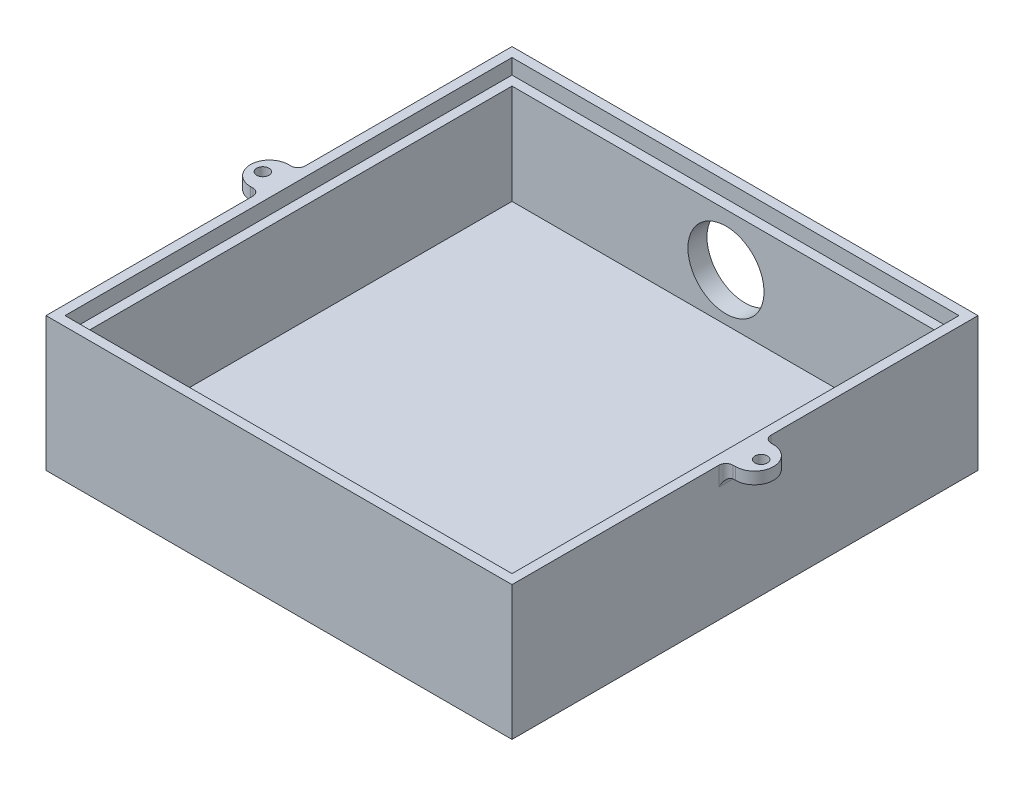
SolidWorks part; units mm, degrees
ref_plane "Front Plane" through (0, 0, 0) normal (0, 0, 1) x (1, 0, 0)
ref_plane "Top Plane" through (0, 0, 0) normal (0, 1, 0) x (1, 0, 0)
ref_plane "Right Plane" through (0, 0, 0) normal (1, 0, 0) x (0, 0, -1)
sketch "Sketch1" plane through (0, 0, 0) normal (0, 1, 0) x (1, 0, 0)
  line L1 (-49, 49) -> (49, 49)
  line L2 (-49, 49) -> (-49, -49)
  line L3 (-49, -49) -> (49, -49)
  line L4 (49, 49) -> (49, -49)
  line L5 (-49, 49) -> (49, -49) construction
  line L6 (-49, -49) -> (49, 49) construction
  point P0 (0, 0)
  dimension "D1" = 98
  dimension "D2" = 98
extrude "Boss-Extrude1" add sketch "Sketch1" along normal blind 30
sketch "Sketch2" plane through (0, 30, 0) normal (0, 1, 0) x (1, 0, 0)
  line L1 (-47, 47) -> (47, 47)
  line L2 (-47, 47) -> (-47, -47)
  line L3 (-47, -47) -> (47, -47)
  line L4 (47, 47) -> (47, -47)
  line L5 (-47, 47) -> (47, -47) construction
  line L6 (-47, -47) -> (47, 47) construction
  point P0 (0, 0)
  dimension "D1" = 94
  dimension "D2" = 94
extrude "Cut-Extrude1" cut sketch "Sketch2" against normal blind 5
sketch "Sketch3" plane through (0, 25, 0) normal (0, 1, 0) x (1, 0, 0)
  line L1 (-45, 45) -> (45, 45)
  line L2 (-45, 45) -> (-45, -45)
  line L3 (-45, -45) -> (45, -45)
  line L4 (45, 45) -> (45, -45)
  line L5 (-45, 45) -> (45, -45) construction
  line L6 (-45, -45) -> (45, 45) construction
  point P0 (0, 0)
  dimension "D1" = 90
  dimension "D2" = 90
extrude "Cut-Extrude2" cut sketch "Sketch3" against normal blind 21
sketch "Sketch4" plane through (0, 30, 0) normal (0, 1, 0) x (1, 0, 0)
  line L1 (-47, 47) -> (47, 47)
  line L2 (-47, 47) -> (-47, -47)
  line L3 (-47, -47) -> (47, -47)
  line L4 (47, 47) -> (47, -47)
  line L5 (-49, 49) -> (49, 49)
  line L6 (-49, 49) -> (-49, -49)
  line L7 (-49, -49) -> (49, -49)
  line L8 (49, 49) -> (49, -49)
extrude "Cut-Extrude3" cut sketch "Sketch4" against normal blind 1.8
sketch "Sketch5" plane through (0, 28.2, 0) normal (0, 1, 0) x (1, 0, 0)
  line L0 (-49, 49) -> (-49, -49) construction
  line L1 (-49, 4) -> (-51, 4)
  line L2 (-49, 4) -> (-49, -4)
  line L3 (-49, -4) -> (-51, -4)
  line L5 (49, 49) -> (-49, 49) construction
  line L7 (0, -8.1636) -> (0, 15.1829) construction
  line L8 (49, 4) -> (49, -4)
  line L9 (49, -4) -> (51, -4)
  line L10 (49, 4) -> (51, 4)
  arc A0 (-51, 4) -> (-51, -4) centre (-51, 0) ccw
  circle A1 centre (-52.4, 0) radius 1.3
  circle A2 centre (52.4, 0) radius 1.3
  arc A3 (51, 4) -> (51, -4) centre (51, 0) cw
  dimension "D4" = 2.6
  dimension "D1" = 2
  dimension "D2" = 8
  dimension "D3" = 45
  dimension "D5" = 3.4
extrude "Boss-Extrude2" add sketch "Sketch5" against normal blind 2.5
fillet "Fillet1" radius 1.5 3 edges at (-49, 26.95, -4) (-49, 25.7, 0) (-49, 26.95, 4)
fillet "Fillet2" radius 1.5 3 edges at (49, 26.95, -4) (49, 25.7, 0) (49, 26.95, 4)
sketch "Sketch6" plane through (0, 0, -49) normal (0, 0, -1) x (-1, 0, 0)
  line L0 (-49, 0) -> (49, 0) construction
  circle A0 centre (0, 14) radius 8
  dimension "D1" = 16
  dimension "D2" = 14
extrude "Cut-Extrude4" cut sketch "Sketch6" against normal up to next
sketch "Sketch7" plane through (0, 0, 0) normal (0, -1, 0) x (1, 0, 0)
  line L3 (-4, -10) -> (-1, -10)
  line L6 (-4, 10) -> (1, 10)
  line L7 (-1, -10) -> (1, -10)
  line L8 (-4, 10) -> (-4, -10)
  line L9 (-49, -49) -> (-49, 49) construction
  arc A0 (1, 0) -> (1, 10) centre (1, 5) ccw
  arc A1 (1, -10) -> (1, 0) centre (1, -5) ccw
  circle A2 centre (1, 5) radius 1.9684
  circle A3 centre (1, -5) radius 1.9684
  dimension "D4" = 10
  dimension "D6" = 10
  dimension "D7" = 5
  dimension "D11" = 3.9367
  dimension "D3" = 45
  dimension "D12" = 5
extrude "Cut-Extrude5" cut sketch "Sketch7" against normal blind 1
